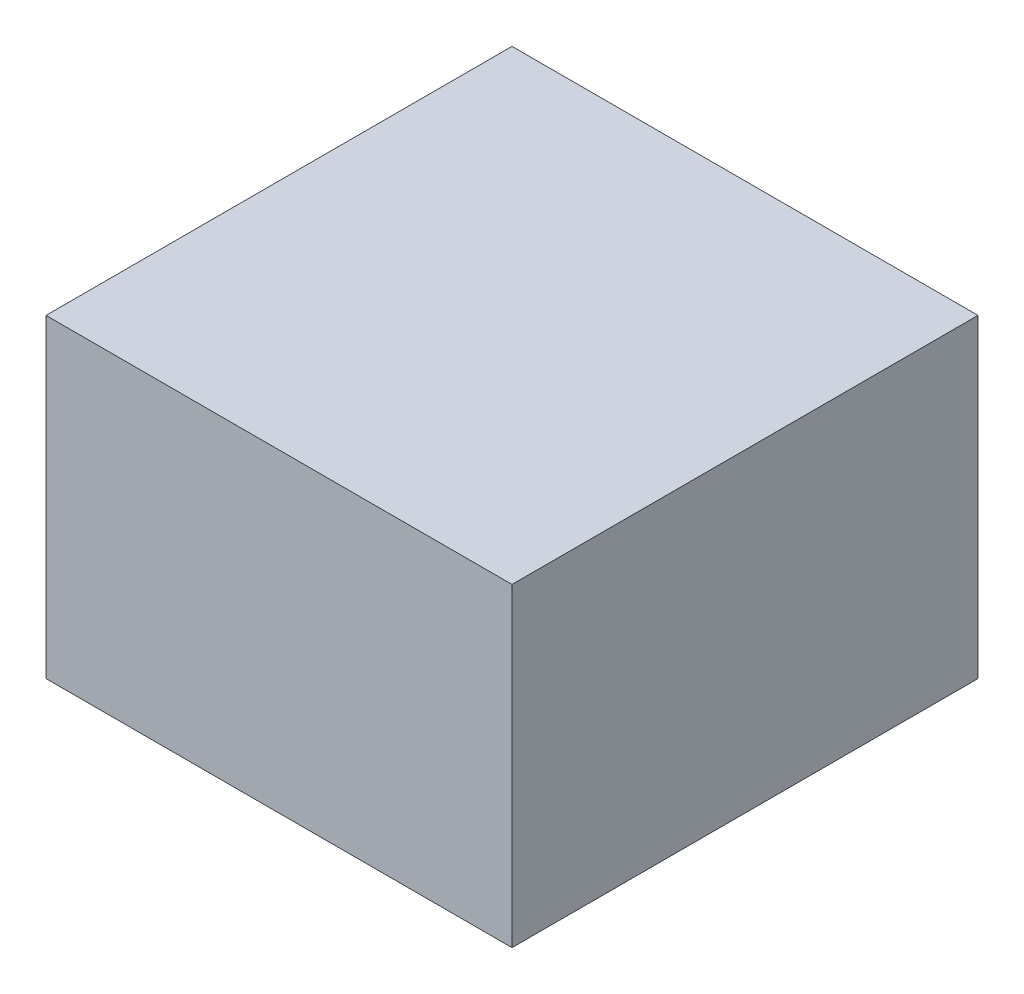
SolidWorks part; units mm, degrees
ref_plane "Plan de face" through (0, 0, 0) normal (0, 0, 1) x (1, 0, 0)
ref_plane "Plan de dessus" through (0, 0, 0) normal (0, 1, 0) x (1, 0, 0)
ref_plane "Plan de droite" through (0, 0, 0) normal (1, 0, 0) x (0, 0, -1)
sketch "Esquisse1" plane through (0, 0, 0) normal (0, 1, 0) x (1, 0, 0)
  line L1 (-17.3023, 18.7907) -> (22.6977, 18.7907)
  line L2 (-17.3023, 18.7907) -> (-17.3023, -21.2093)
  line L3 (-17.3023, -21.2093) -> (22.6977, -21.2093)
  line L4 (22.6977, 18.7907) -> (22.6977, -21.2093)
  dimension "D1" = 40
  dimension "D2" = 40
extrude "Boss.-Extru.1" add sketch "Esquisse1" along normal blind 27
